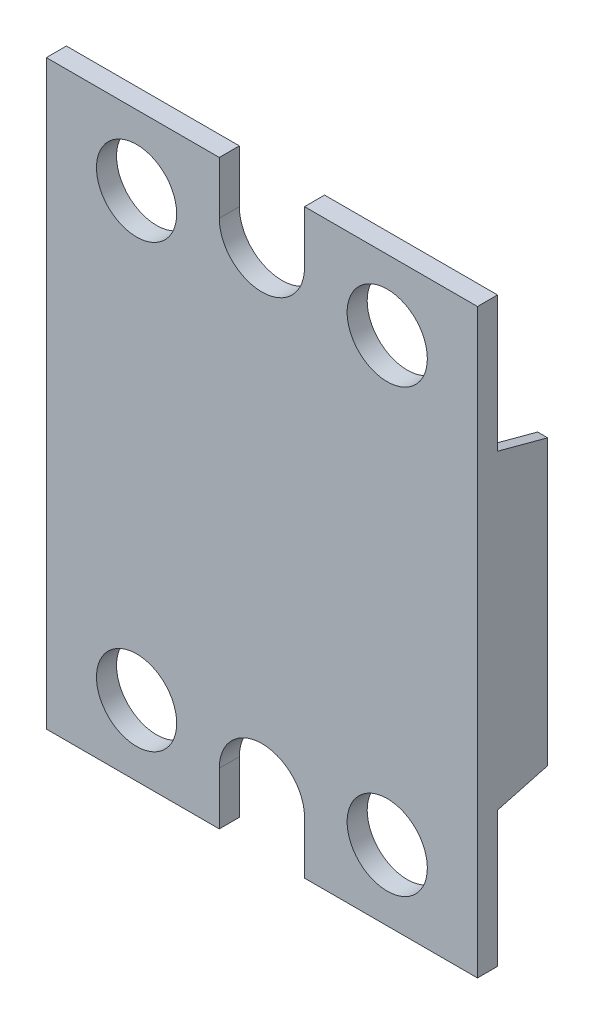
SolidWorks part; units mm, degrees
material "Acrylic (Medium-high impact)"
ref_plane "Front Plane" through (0, 0, 0) normal (0, 0, 1) x (1, 0, 0)
ref_plane "Top Plane" through (0, 0, 0) normal (0, 1, 0) x (1, 0, 0)
ref_plane "Right Plane" through (0, 0, 0) normal (1, 0, 0) x (0, 0, -1)
ref_plane "Plane1" through (0, 0, -2) normal (0, 0, -1) x (-1, 0, 0)
sketch "Sketch1" plane through (0, 0, -2) normal (0, 0, -1) x (-1, 0, 0)
  line L0 (21.5, -29) -> (21.5, 29)
  line L1 (21.5, 29) -> (-21.5, 29)
  line L2 (-21.5, 29) -> (-21.5, -29)
  line L3 (-21.5, -29) -> (21.5, -29)
extrude "Boss-Extrude1" add sketch "Sketch1" against normal blind 2
sketch "Sketch2" plane through (0, 0, 0) normal (0, 0, 1) x (1, 0, 0)
  line L0 (4.25, 29) -> (-4.25, 29)
  line L1 (-4.25, 29) -> (-4.25, 23.75)
  line L2 (4.25, 23.75) -> (4.25, 29)
  arc A0 (-4.25, 23.75) -> (4.25, 23.75) centre (0, 23.75) ccw
extrude "Cut-Extrude1" cut sketch "Sketch2" against normal through all
sketch "Sketch3" plane through (0, 0, 0) normal (0, 0, 1) x (1, 0, 0)
  line L0 (-4.25, -29) -> (4.25, -29)
  line L1 (4.25, -29) -> (4.25, -23.75)
  line L2 (-4.25, -23.75) -> (-4.25, -29)
  arc A0 (4.25, -23.75) -> (-4.25, -23.75) centre (0, -23.75) ccw
extrude "Cut-Extrude2" cut sketch "Sketch3" against normal through all
sketch "Sketch4" plane through (0, 0, -2) normal (0, 0, -1) x (-1, 0, 0)
  line L0 (-21.5, -15.5) -> (-21.5, 15.5)
  line L1 (-21.5, 15.5) -> (-20.5, 15.5)
  line L2 (-20.5, 15.5) -> (-20.5, -15.5)
  line L3 (-20.5, -15.5) -> (-21.5, -15.5)
extrude "Boss-Extrude2" add sketch "Sketch4" along normal blind 5
sketch "Sketch5" plane through (0, 0, -2) normal (0, 0, -1) x (-1, 0, 0)
  line L0 (21.5, 15.5) -> (21.5, -15.5)
  line L1 (21.5, -15.5) -> (20.5, -15.5)
  line L2 (20.5, -15.5) -> (20.5, 15.5)
  line L3 (20.5, 15.5) -> (21.5, 15.5)
extrude "Boss-Extrude3" add sketch "Sketch5" along normal blind 5
draft "Draft1" type of draft neutral plane draft angle 15 faces to draft 4 face at (21.125, -15.5, -5.125) face at (20.875, 15.5, -5.125) face at (-21, 15.5, -4.5) face at (-21, -15.5, -4.5) neutral plane through (0, 0, -2) neutral plane normal (0, 0, -1) parameters "D1"=15
hole_wizard "Ø8.0 (8) Diameter Hole1" positions "Sketch7" profile "Sketch6" hole size "Ø8.0" standard "ANSI Metric"
sketch "Sketch7" plane through (0, 0, 0) normal (0, 0, 1) x (1, 0, 0)
  point P0 (12.5, 22)
  point P1 (-12.5, 22)
  point P2 (-12.5, -22)
  point P3 (12.5, -22)
sketch "Sketch6" plane through (12.5, 22, 0) normal (1, 0, 0) x (0, -1, 0)
  line L0 (0, 0) -> (0, 7)
  line L1 (0, 7) -> (4, 7)
  line L2 (4, 7) -> (4, 0)
  line L5 (4, 0) -> (0, 0)
  line L11 (0, -6.35) -> (0, 107.95) construction
  dimension "Thru Hole Dia." = 8
  dimension "Thru Hole Depth" = 7
